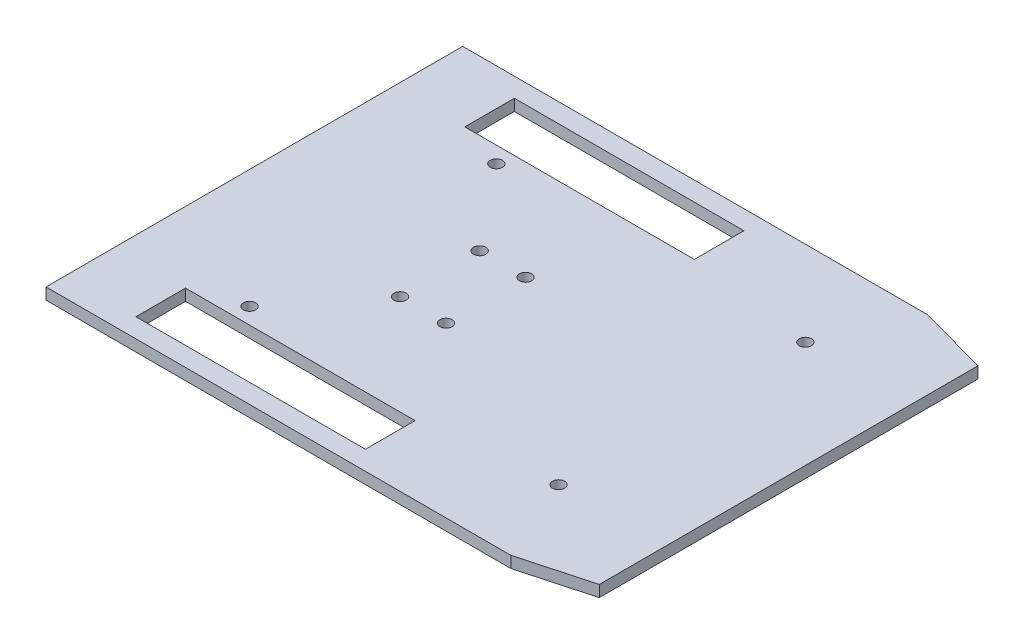
SolidWorks part; units mm, degrees
ref_plane "Front Plane" through (0, 0, 0) normal (0, 0, 1) x (1, 0, 0)
ref_plane "Top Plane" through (0, 0, 0) normal (0, 1, 0) x (1, 0, 0)
ref_plane "Right Plane" through (0, 0, 0) normal (1, 0, 0) x (0, 0, -1)
sketch "Sketch1" plane through (0, 0, 0) normal (0, 1, 0) x (1, 0, 0)
  line L1 (0, 0) -> (110, 0)
  line L2 (0, 0) -> (0, 90)
  line L3 (0, 90) -> (110, 90)
  line L4 (110, 0) -> (110, 90)
  dimension "D1" = 90
  dimension "D2" = 110
extrude "Boss-Extrude1" add sketch "Sketch1" along normal blind 3
sketch "Sketch2" plane through (0, 3, 0) normal (0, 1, 0) x (1, 0, 0)
  line L0 (110, 90) -> (0, 90) construction
  line L1 (0, 90) -> (0, 0) construction
  line L2 (40, 55.4) -> (39.7079, 55.4)
  line L3 (0, 81.5) -> (70, 81.5)
  line L4 (70, 81.5) -> (70, 90)
  line L5 (0, 62.9) -> (52.7636, 62.9)
  line L6 (0, 90) -> (0, 0)
  line L7 (0, 45) -> (-10.1917, 45)
  line L8 (70, 8.5) -> (70, 0)
  line L9 (0, 8.5) -> (70, 8.5)
  line L10 (40, 0.815) -> (40, 0)
  line L12 (38.24, 0.815) -> (41.76, 0.815) construction
  line L13 (40, 0) -> (70, 0)
  line L14 (40, 0.815) -> (10, 0.815)
  line L15 (10, 0.815) -> (10, 8.5)
  line L16 (10, 0.815) -> (10, 0)
  line L17 (0, 0) -> (110, 0) construction
  line L18 (10, 89.185) -> (10, 90)
  line L19 (10, 89.185) -> (10, 81.5)
  circle A0 centre (40, 55.4) radius 1.6
  circle A1 centre (52, 55.4) radius 1.6
  circle A2 centre (52, 34.6) radius 1.6
  circle A3 centre (40, 34.6) radius 1.6
  dimension "D1" = 3.2
  dimension "D2" = 3.2
  dimension "D3" = 18.6
  dimension "D4" = 30
  dimension "25" = 40
  dimension "D5" = 12
  dimension "D6" = 8.5
  dimension "D7" = 7.5
  dimension "D8" = 30
extrude "Cut-Extrude1" cut sketch "Sketch2" against normal blind 3
sketch "Sketch3" plane through (0, 3, 0) normal (0, 1, 0) x (1, 0, 0)
  line L0 (0, 81.5) -> (0, 8.5)
  line L1 (0, 45) -> (12.8836, 45)
sketch "Sketch4" plane through (0, 3, 0) normal (0, 1, 0) x (1, 0, 0)
  line L0 (0, 45) -> (0, 12.74)
  line L1 (0, 45) -> (12.8836, 45) construction
  line L2 (0, 45) -> (12.8836, 45)
  line L8 (0, 90) -> (0, 0)
  line L9 (0, 90) -> (0, 0)
  line L10 (70, 90) -> (70, 81.5)
  line L11 (10, 8.5) -> (70, 8.5)
  line L12 (70, 8.5) -> (70, 0)
  line L13 (70, 90) -> (70, 81.5)
  line L15 (70, 81.5) -> (10, 81.5)
  line L19 (10, 8.5) -> (70, 8.5)
  line L20 (70, 8.5) -> (70, 0)
  line L29 (0, 0) -> (10, 0)
  line L30 (0, 0) -> (10, 0)
  line L31 (70, 81.5) -> (10, 81.5)
  line L35 (70, 0) -> (110, 0)
  line L36 (70, 0) -> (110, 0)
  line L37 (110, 0) -> (110, 90)
  line L38 (110, 0) -> (110, 90)
  line L39 (110, 90) -> (70, 90)
  line L40 (110, 90) -> (70, 90)
  line L41 (10, 0) -> (10, 8.5)
  line L42 (10, 0) -> (10, 8.5)
  line L46 (10, 81.5) -> (10, 90)
  line L47 (10, 81.5) -> (10, 90)
  line L48 (10, 90) -> (0, 90)
  line L49 (10, 90) -> (0, 90)
  circle A0 centre (22.5, 12.74) radius 1.6
  circle A1 centre (103.27, 12.74) radius 1.6
  circle A2 centre (103.27, 77.26) radius 1.6
  circle A3 centre (22.5, 77.26) radius 1.6
  circle A4 centre (40, 34.6) radius 1.6 construction
  dimension "D3" = 3.2
  dimension "D5" = 3.2
  dimension "D2" = 32.26
  dimension "D4" = 17.5
  dimension "D6" = 32.26
  dimension "D7" = 80.77
  dimension "D1" = 0
extrude "Cut-Extrude2" cut sketch "Sketch4" against normal blind 10 contours A3 | A0 | A1 | A2
sketch "Esquisse1" plane through (0, 3, 0) normal (0, 1, 0) x (1, 0, 0)
  line L0 (10, 0) -> (10, -4.4661)
  line L1 (10, -4.4661) -> (70, -4.4661)
  line L2 (70, -4.4661) -> (70, 0)
  line L5 (113, -9.4661) -> (-8.5, -9.4661)
  line L6 (-8.5, -9.4661) -> (-8.5, -4.4661)
  line L12 (0, 45) -> (110, 45) construction
  line L13 (0, 90) -> (0, 0) construction
  line L14 (110, 0) -> (110, 90) construction
  line L15 (131.1653, 94.5) -> (113, 99.4661)
  line L17 (-8.5, 99.4661) -> (-8.5, 94.4661)
  line L28 (110, 0) -> (70, 0)
  line L40 (131.1653, -4.5) -> (131.1653, 94.5)
  line L43 (-8.5, -4.4661) -> (-8.5, 94.4661)
  line L45 (10, 0) -> (0, 0)
  line L46 (0, 0) -> (0, 90)
  line L47 (0, 90) -> (10, 90)
  line L48 (110, 90) -> (110, 0)
  line L50 (134.1653, 94.4661) -> (134.1653, -4.4661) construction
  line L51 (-8.5, 94.4661) -> (-8.5, -4.4661) construction
  line L57 (131.1653, -4.5) -> (113, -9.4661)
  line L58 (113, 99.4661) -> (-8.5, 99.4661)
  line L59 (70, 94.4661) -> (70, 90)
  line L60 (10, 94.4661) -> (70, 94.4661)
  line L61 (10, 90) -> (10, 94.4661)
  line L62 (110, 90) -> (70, 90)
  point P28 (119.1688, 94.5)
  dimension "D1" = 5
  dimension "D2" = 3
  dimension "D3" = 9.4661
  dimension "D4" = 3
extrude "Boss.-Extru.1" add sketch "Esquisse1" against normal blind 3
